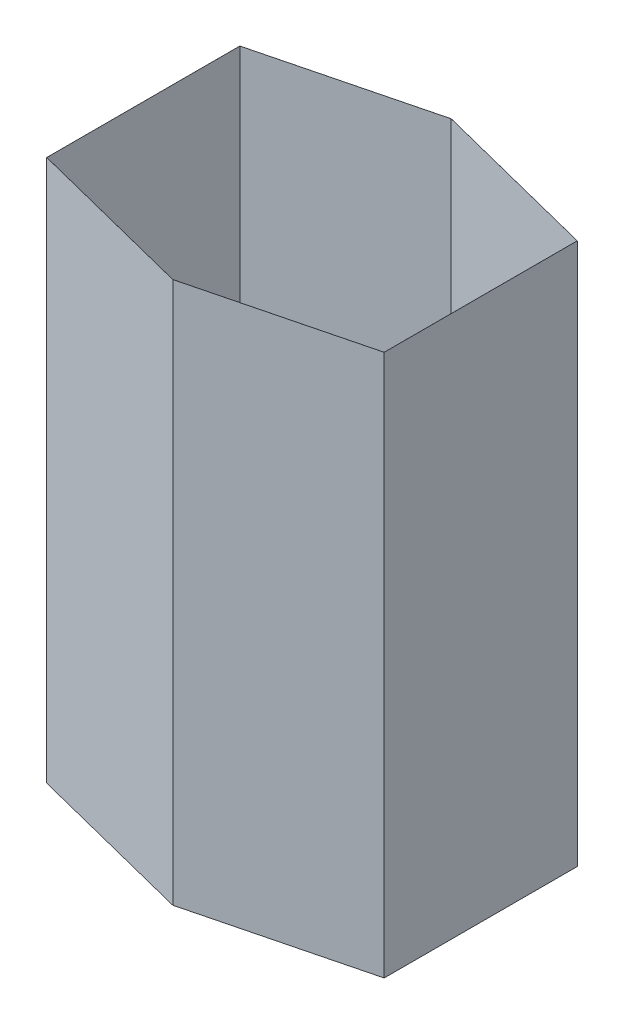
SolidWorks part; units mm, degrees
ref_plane "Plan de face" through (0, 0, 0) normal (0, 0, 1) x (1, 0, 0)
ref_plane "Plan de dessus" through (0, 0, 0) normal (0, 1, 0) x (1, 0, 0)
ref_plane "Plan de droite" through (0, 0, 0) normal (1, 0, 0) x (0, 0, -1)
sketch "Esquisse2" plane through (0, 0, 0) normal (0, 1, 0) x (1, 0, 0)
  line L0 (-89.7864, 0) -> (128.1449, 0) construction
  line L1 (19.1793, 89.9225) -> (19.1793, -105.9325) construction
  line L2 (-89.7864, -62.35) -> (-89.7864, 62.35)
  line L3 (-89.7864, 62.35) -> (19.1793, 89.9225)
  line L4 (-89.7864, -62.35) -> (19.1793, -89.9225)
  line L5 (128.1449, -62.35) -> (19.1793, -89.9225)
  line L6 (128.1449, -62.35) -> (128.1449, 62.35)
  line L7 (128.1449, 62.35) -> (19.1793, 89.9225)
extrude "Extru.-Mince1" add sketch "Esquisse2" along normal blind 350 thin thin type one direction wall 0.01
